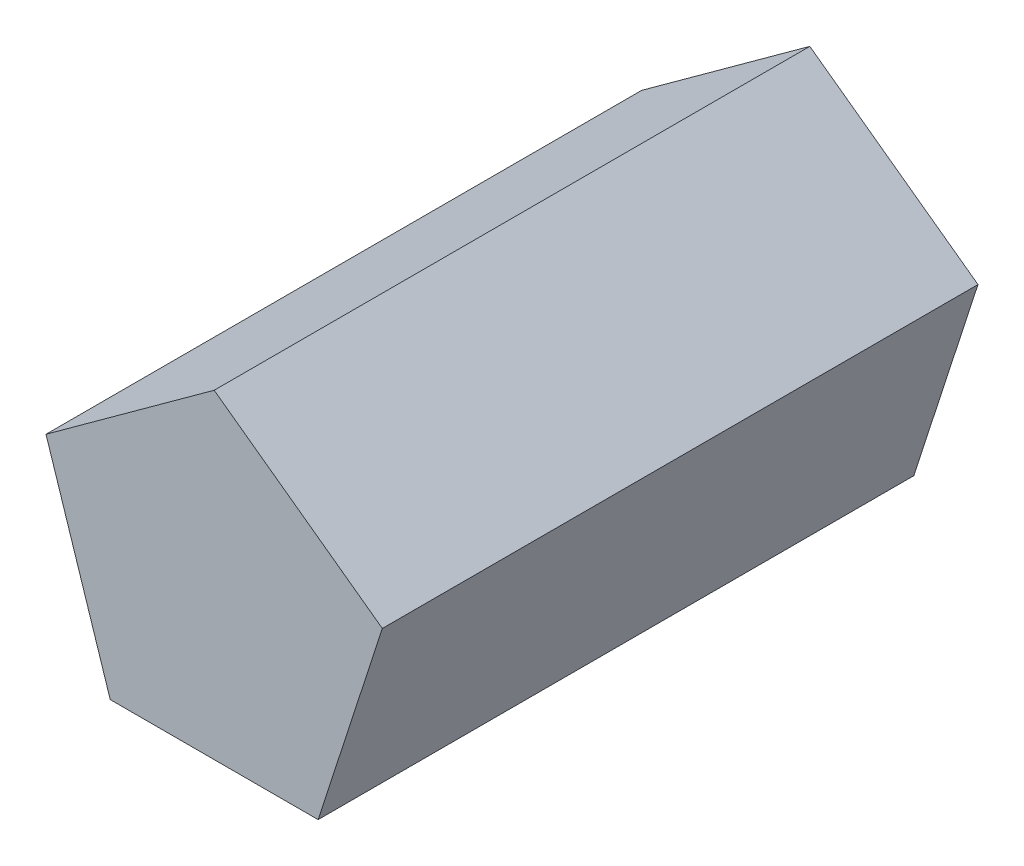
SolidWorks part; units mm, degrees
ref_plane "Piano frontale" through (0, 0, 0) normal (0, 0, 1) x (1, 0, 0)
ref_plane "Piano superiore" through (0, 0, 0) normal (0, 1, 0) x (1, 0, 0)
ref_plane "Piano destro" through (0, 0, 0) normal (1, 0, 0) x (0, 0, -1)
sketch "Schizzo1" plane through (0, 0, 0) normal (0, 0, 1) x (1, 0, 0)
  line L1 (27.9198, -38.4283) -> (45.1752, 14.6783)
  line L2 (45.1752, 14.6783) -> (0, 47.5)
  line L3 (0, 47.5) -> (-45.1752, 14.6783)
  line L4 (-45.1752, 14.6783) -> (-27.9198, -38.4283)
  line L5 (-27.9198, -38.4283) -> (27.9198, -38.4283)
  circle A0 centre (0, 0) radius 38.4283 construction
  dimension "D1" = 47.5
extrude "Estrusione-Estrusione1" add sketch "Schizzo1" along normal blind 160
